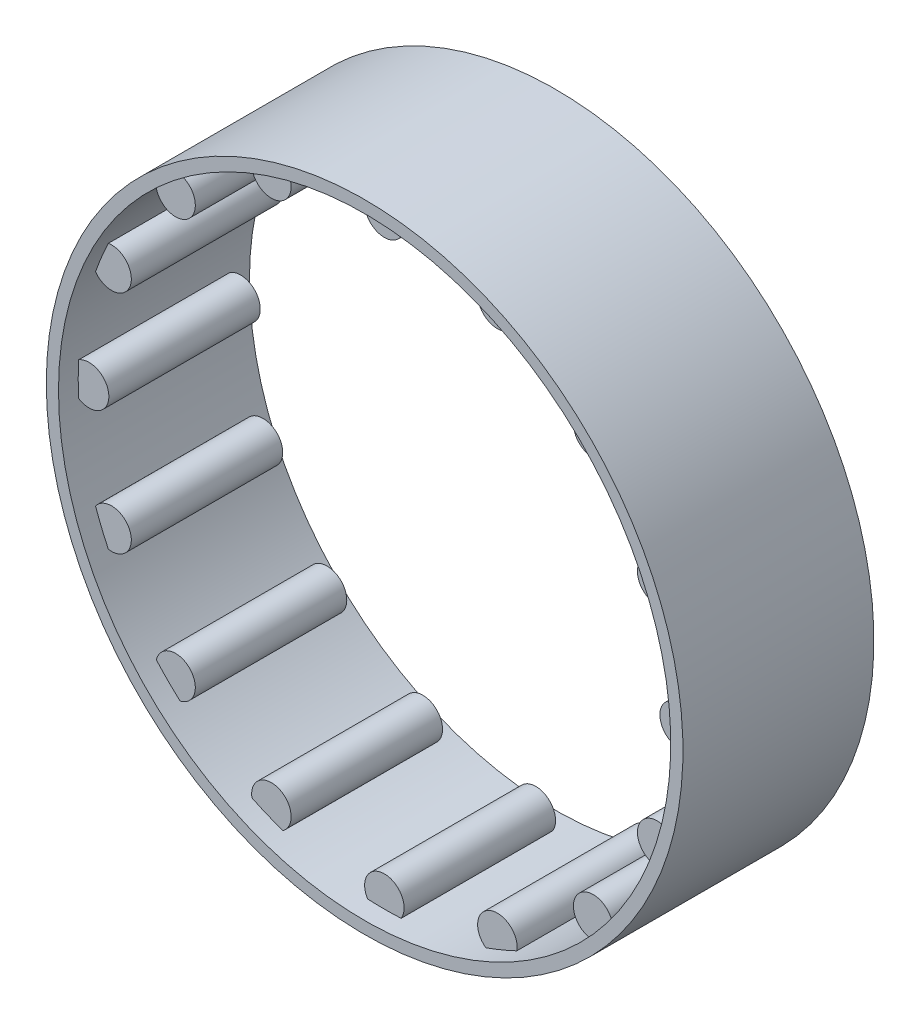
SolidWorks part; units mm, degrees
ref_plane "Front Plane" through (0, 0, 0) normal (0, 0, 1) x (1, 0, 0)
ref_plane "Top Plane" through (0, 0, 0) normal (0, 1, 0) x (1, 0, 0)
ref_plane "Right Plane" through (0, 0, 0) normal (1, 0, 0) x (0, 0, -1)
sketch "Sketch1" plane through (0, 0, 0) normal (0, 0, 1) x (1, 0, 0)
  circle A1 centre (0, 44.85) radius 3
  circle A2 centre (17.1634, 41.436) radius 3
  circle A3 centre (31.7137, 31.7137) radius 3
  circle A4 centre (41.436, 17.1634) radius 3
  circle A5 centre (44.85, 0) radius 3
  circle A6 centre (41.436, -17.1634) radius 3
  circle A7 centre (31.7137, -31.7137) radius 3
  circle A8 centre (17.1634, -41.436) radius 3
  circle A9 centre (0, -44.85) radius 3
  circle A10 centre (-17.1634, -41.436) radius 3
  circle A11 centre (-31.7137, -31.7137) radius 3
  circle A12 centre (-41.436, -17.1634) radius 3
  circle A13 centre (-44.85, 0) radius 3
  circle A14 centre (-41.436, 17.1634) radius 3
  circle A15 centre (-31.7137, 31.7137) radius 3
  circle A16 centre (-17.1634, 41.436) radius 3
  circle A17 centre (0, 0) radius 47.85
  point P37 (0, 0)
  dimension "D2" = 6
  dimension "D3" = 16
extrude "Boss-Extrude2" add sketch "Sketch1" along normal blind 29 contours A14 | A15 | A16 | A1 | A2 | A3 | A4 | A5 | A6 | A8 | A9 | A10 | A12 | A11 | A13 | A7
sketch "Sketch2" plane through (0, 0, 0) normal (0, 0, -1) x (-1, 0, 0)
  circle A0 centre (0, 0) radius 47.85
  circle A1 centre (-31.7137, 31.7137) radius 3 construction
  circle A2 centre (0, 0) radius 46.5
  dimension "D1" = 93
extrude "Boss-Extrude4" add sketch "Sketch2" against normal blind 29 separate body
sketch "Sketch3" plane through (0, 0, 0) normal (0, 0, -1) x (-1, 0, 0)
  circle A0 centre (0, 0) radius 46.5
extrude "Cut-Extrude1" cut sketch "Sketch3" against normal blind 3 contours A0
sketch "Sketch4" plane through (0, 0, 29) normal (0, 0, 1) x (1, 0, 0)
  circle A0 centre (0, 0) radius 46.5
extrude "Cut-Extrude2" cut sketch "Sketch4" against normal blind 3
sketch "Sketch5" plane through (0, 0, 0) normal (0, 0, -1) x (-1, 0, 0)
  circle A0 centre (0, 0) radius 47.85
  circle A1 centre (0, 0) radius 48.35
  dimension "D1" = 0.5
extrude "Boss-Extrude6" add sketch "Sketch5" against normal blind 29
